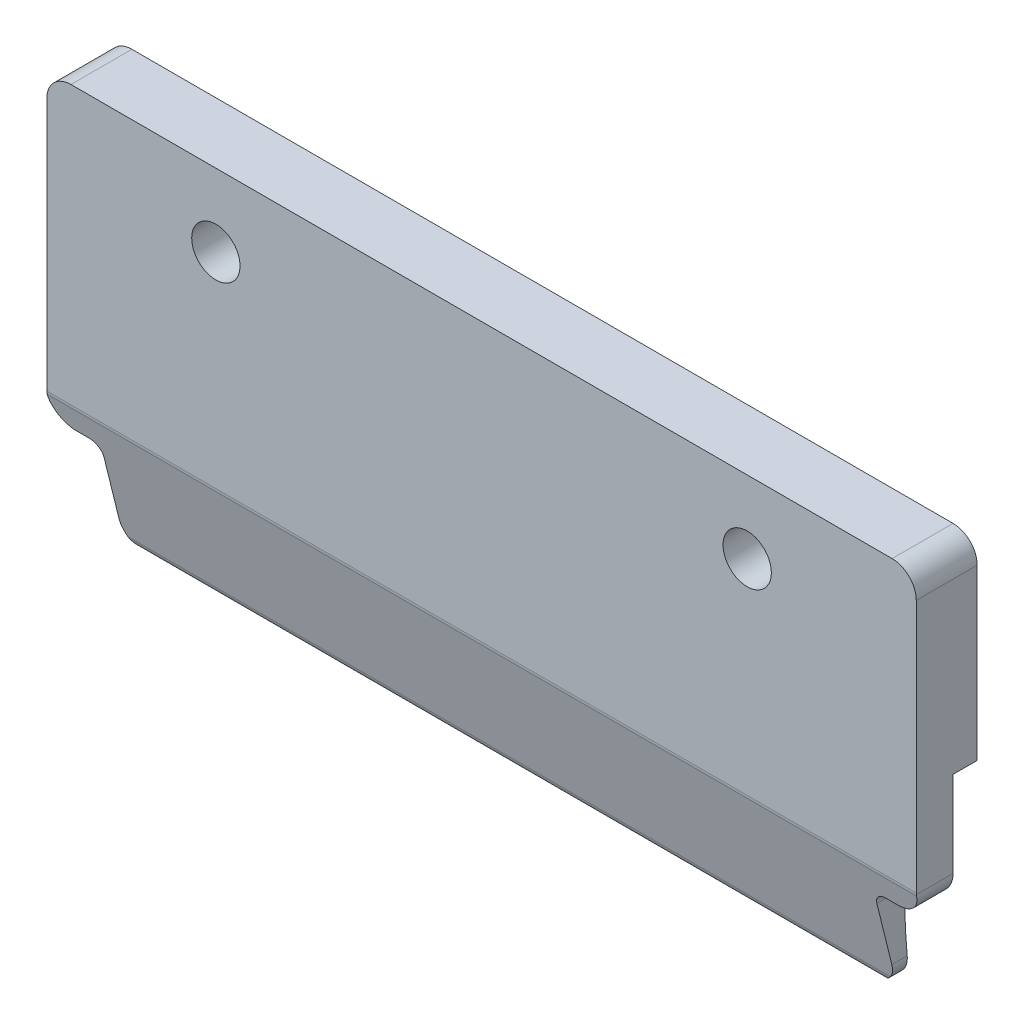
SolidWorks part; units mm, degrees
ref_plane "Front Plane" through (0, 0, 0) normal (0, 0, 1) x (1, 0, 0)
ref_plane "Top Plane" through (0, 0, 0) normal (0, 1, 0) x (1, 0, 0)
ref_plane "Right Plane" through (0, 0, 0) normal (1, 0, 0) x (0, 0, -1)
sketch "Sketch1" plane through (0, 0, 0) normal (0, 0, 1) x (1, 0, 0)
  line L1 (-18, 9.3045) -> (-18, 10.3045)
  line L2 (18, 9.3035) -> (18, 17.3035)
  line L3 (18, 9.3035) -> (18, 6.7512)
  line L4 (-18, 10.3045) -> (-18, 17.3035)
  line L5 (17, 5.7512) -> (16.5, 5.7512)
  line L6 (16, 5.2512) -> (16, 2.7512)
  line L7 (15, 1.7512) -> (-15, 1.7512)
  line L9 (17, 18.3035) -> (-17, 18.3035)
  line L10 (-16, 5.2512) -> (-16, 2.7512)
  line L11 (-17, 5.7512) -> (-16.5, 5.7512)
  line L12 (-18, 9.3045) -> (-18, 6.7512)
  arc A0 (18, 6.7512) -> (17, 5.7512) centre (17, 6.7512) cw
  arc A2 (16, 2.7512) -> (15, 1.7512) centre (15, 2.7512) cw
  arc A3 (16, 5.2512) -> (16.5, 5.7512) centre (16.5, 5.2512) cw
  arc A4 (-16, 5.2512) -> (-16.5, 5.7512) centre (-16.5, 5.2512) ccw
  arc A5 (-16, 2.7512) -> (-15, 1.7512) centre (-15, 2.7512) ccw
  arc A7 (-18, 6.7512) -> (-17, 5.7512) centre (-17, 6.7512) ccw
  arc A8 (18, 17.3035) -> (17, 18.3035) centre (17, 17.3035) ccw
  arc A9 (-18, 17.3035) -> (-17, 18.3035) centre (-17, 17.3035) cw
  point P37 (-16, 5.7512)
  point P38 (-18, 10.3045)
  point P39 (-18, 5.7512)
  dimension "D1" = 1
extrude "Boss-Extrude1" add sketch "Sketch1" along normal blind 1.5 and the other way blind 1.2
sketch "Sketch3" plane through (18, 0, 0) normal (1, 0, 0) x (0, 0, -1)
  line L1 (0.0238, 5.7545) -> (0.0238, 10.3045)
  line L3 (0.2373, 1.7512) -> (0.1268, 1.7512)
  line L4 (0.0238, 10.3045) -> (1.0238, 10.3045)
  line L7 (-1.5, 6.812) -> (-1.5, 1.7512)
  line L9 (0.2373, 1.7512) -> (1.2709, 1.7512)
  line L10 (1.2, 1.7512) -> (-1.5, 1.7512) construction
  line L11 (-1.5, 10.3045) -> (0.0238, 10.3045)
  line L12 (1.2709, 1.7512) -> (1.2709, 10.3045)
  line L13 (0.0238, 10.3045) -> (-1.5, 10.3045)
  line L14 (-1.5, 10.3045) -> (-1.5, 6.812)
  line L15 (-1.4854, 6.6921) -> (-0.3586, 2.1312)
  line L17 (-1.5, 1.7512) -> (0.1268, 1.7512)
  line L18 (0.0238, 10.3051) -> (0.0238, 10.3045)
  line L19 (1, 10.3051) -> (-1.5, 10.3051) construction
  line L20 (1.0238, 10.3045) -> (1.0238, 22.6808)
  line L21 (1.2709, 10.3045) -> (1.2709, 10.3051)
  arc A0 (0.0238, 5.7545) -> (0.2373, 1.7512) centre (25.9469, 5.1296) ccw
  arc A2 (-1.5, 6.812) -> (-1.4854, 6.6921) centre (-1, 6.812) ccw
  arc A3 (-0.3586, 2.1312) -> (0.1268, 1.7512) centre (0.1268, 2.2512) ccw
  arc A4 (1.0238, 22.6808) -> (1.2709, 10.3051) centre (1.0238, 16.4905) cw
  point P28 (-1.5, 6.7512)
  point P31 (-0.2647, 1.7512)
  dimension "D1" = 4.55
extrude "Cut-Extrude1" cut sketch "Sketch3" against normal blind 40
sketch "Sketch6" plane through (-18, 0, 0) normal (-1, 0, 0) x (0, 0, 1)
  line L0 (-1.0238, 10.3045) -> (-1.0238, 12.6345)
  line L1 (-1.0238, 17.3035) -> (-1.0238, 10.3045) construction
sketch "Sketch7" plane through (-18, 0, 0) normal (-1, 0, 0) x (0, 0, 1)
  line L0 (-1.0238, 10.3045) -> (1.3872, 3.6805)
  line L1 (-1.0238, 10.3045) -> (-1.0238, 12.6345)
  line L2 (-1.0238, 17.3035) -> (-1.0238, 10.3045) construction
sketch "Sketch8" plane through (0, 0, -1.0238) normal (0, 0, -1) x (-1, 0, 0)
  line L1 (0, 10.3045) -> (0, 12.6345)
  line L2 (18, 10.3045) -> (-18, 10.3045) construction
  line L3 (0, 12.6345) -> (0, 13.8645)
  circle A0 centre (0, 13.8645) radius 1.23
sketch "Sketch10" plane through (18, 0, 0) normal (1, 0, 0) x (0, 0, -1)
  line L1 (1.0238, 10.3045) -> (1.0238, 17.3035) construction
  line L2 (1.0238, 13.804) -> (12.7887, 9.5219) construction
sketch "Sketch11" plane through (0, 0, -1.0238) normal (0, 0, -1) x (-1, 0, 0)
  line L0 (0, 10.3045) -> (0, 15.2945)
  line L2 (18, 10.3045) -> (-18, 10.3045) construction
  line L3 (-11, 15.2945) -> (11, 15.2945)
  circle A0 centre (11, 15.2945) radius 1
  circle A1 centre (-11, 15.2945) radius 1
  circle A2 centre (0, 15.2945) radius 2.5
  point P9 (0, 0)
  dimension "D1" = 2
  dimension "D4" = 5
  dimension "D2" = 11
  dimension "D3" = 4.99
sketch "Sketch12" plane through (18, 0, 0) normal (1, 0, 0) x (0, 0, -1)
  line L0 (1.0238, 10.3045) -> (1.0238, 15.2945)
  line L1 (1.0238, 10.3045) -> (1.0238, 17.3035) construction
  line L2 (1.0238, 15.2945) -> (6.2899, 13.3778)
  dimension "D1" = 4.99
ref_plane "Plane1" through (0, 0.8764, 2.4078) normal (0, -0.342, -0.9397) x (1, 0, 0)
sketch "Sketch15" plane through (0, 0.8764, 2.4078) normal (0, -0.342, -0.9397) x (1, 0, 0)
  line L0 (0, -10.0333) -> (0, -15.0333)
  line L1 (-18, -10.0333) -> (18, -10.0333) construction
  circle A1 centre (0, -15.0333) radius 2.45
  dimension "D2" = 4.9
  dimension "D1" = 5
sketch "Sketch16" plane through (0, 0, 0) normal (1, 0, 0) x (0, 0, -1)
  line L0 (1.0238, 10.3045) -> (1.0238, 15.3085)
  line L1 (1.0238, 10.3045) -> (1.0238, 17.3035) construction
  line L2 (1.0238, 15.3085) -> (6.662, 13.2563)
  line L3 (1.0238, 15.3085) -> (1.0238, 12.8065)
  line L5 (6.662, 10.7613) -> (6.662, 13.2563)
  line L6 (6.662, 10.7613) -> (1.0238, 12.8065)
  dimension "D1" = 2.495
revolve "Revolve1" [suppressed] add sketch "Sketch16" angle 360 about L2
sketch "Sketch17" plane through (0, 0, -1.0238) normal (0, 0, -1) x (-1, 0, 0)
sketch "Sketch18" [suppressed] plane through (0, 0, 0) normal (1, 0, 0) x (0, 0, -1)
  line L0 (1.0238, 15.3085) -> (1.0238, 17.8035)
  line L1 (1.0238, 17.3035) -> (1.0238, 18.3035) construction
  line L2 (1.0238, 17.8035) -> (2.632, 17.2251)
  line L4 (1.0238, 15.3085) -> (7.4638, 12.9645)
  line L5 (6.662, 10.7613) -> (8.2657, 15.1676) construction
  line L6 (2.632, 17.2251) -> (1.8279, 15.0158)
  line L7 (1.0238, 12.8065) -> (2.632, 17.2251) construction
  line L8 (2.632, 17.2251) -> (1.0238, 15.3085)
  dimension "D1" = 2.495
ref_plane "Plane2" through (0, 0, -1.0238) normal (0, 0, -1) x (-1, 0, 0)
extrude "Cut-Extrude2" cut sketch "Sketch11" against normal blind 5
